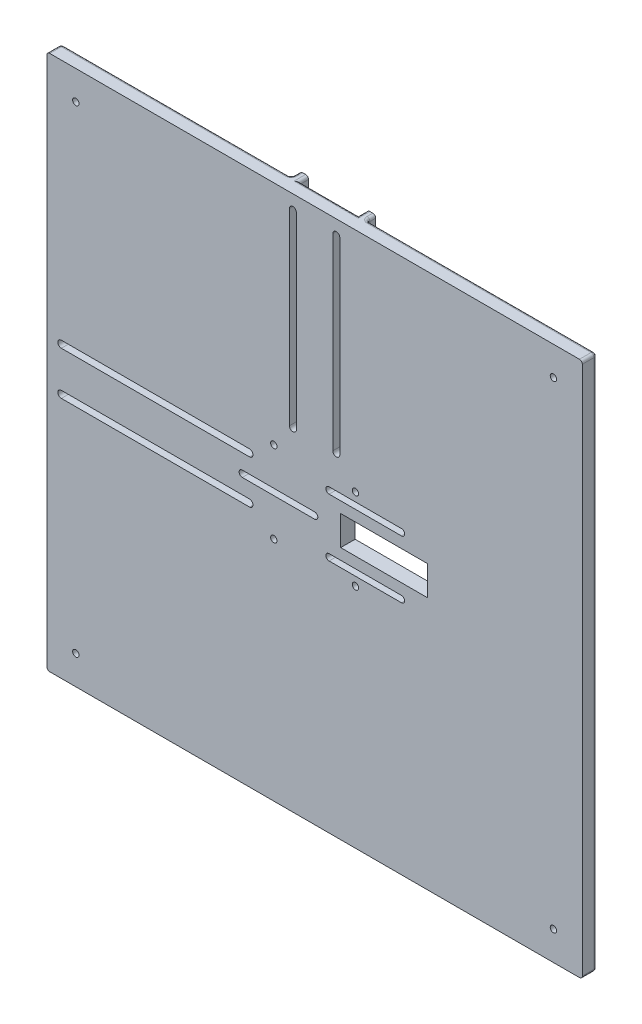
SolidWorks part; units mm, degrees
ref_plane "Plan de face" through (0, 0, 0) normal (0, 0, 1) x (1, 0, 0)
ref_plane "Plan de dessus" through (0, 0, 0) normal (0, 1, 0) x (1, 0, 0)
ref_plane "Plan de droite" through (0, 0, 0) normal (1, 0, 0) x (0, 0, -1)
sketch "Esquisse1" plane through (0, 0, 0) normal (0, 0, 1) x (1, 0, 0)
  line L1 (-92.5, 92.5) -> (92.5, 92.5)
  line L2 (-92.5, 92.5) -> (-92.5, -92.5)
  line L3 (-92.5, -92.5) -> (92.5, -92.5)
  line L4 (92.5, 92.5) -> (92.5, -92.5)
  dimension "D1" = 185
  dimension "D2" = 185
  dimension "D3" = 92.5
  dimension "D4" = 92.5
extrude "Boss.-Extru.1" add sketch "Esquisse1" along normal blind 5
sketch "Esquisse2" plane through (0, 0, 0) normal (0, 0, -1) x (-1, 0, 0)
  line L1 (22.5, 10.1) -> (92.5, 10.1)
  line L4 (92.5, 10.1) -> (92.5, 13.1)
  line L5 (92.5, -13.1) -> (22.5, -13.1)
  line L6 (92.5, -13.1) -> (92.5, -10.1)
  line L7 (92.5, -10.1) -> (22.5, -10.1)
  line L19 (92.5, 92.5) -> (92.5, -92.5) construction
  line L24 (13.1, 22.5) -> (13.1, 92.5)
  line L25 (-92.5, 92.5) -> (92.5, 92.5) construction
  line L26 (10.1, 22.5) -> (10.1, 92.5)
  line L28 (-13.1, 92.5) -> (-10.1, 92.5)
  line L29 (10.1, 92.5) -> (13.1, 92.5)
  line L31 (-10.1, 92.5) -> (-10.1, 22.5)
  line L32 (-13.1, 92.5) -> (-13.1, 22.5)
  line L33 (-10.1, 22.5) -> (-13.1, 22.5)
  line L35 (22.5, -10.1) -> (22.5, -13.1)
  line L36 (92.5, 13.1) -> (22.5, 13.1)
  line L37 (22.5, 13.1) -> (22.5, 10.1)
  line L38 (13.1, 22.5) -> (10.1, 22.5)
  dimension "D1" = 20.2
  dimension "D2" = 3
  dimension "D3" = 3
  dimension "D4" = 10.1
  dimension "D5" = 3
  dimension "D6" = 3
  dimension "D7" = 20.2
  dimension "D8" = 10.1
  dimension "D9" = 70
  dimension "D10" = 70
extrude "Boss.-Extru.2" add sketch "Esquisse2" along normal blind 3
fillet "Congé1" radius 1 32 edges at (-13.1, 57.5, 0) (-57.5, -13.1, 0) (-13.1, 92.5, -1.5) (-92.5, -13.1, -1.5) (92.5, -92.5, 2.5) (92.5, 92.5, 2.5) (92.5, 0, 0) (0, 92.5, 0) (-92.5, 0, 0) (-52.8, 92.5, 0) (-92.5, 52.8, 0) (-92.5, 92.5, 2.5) (52.8, 92.5, 0) (0, -92.5, 0) (-92.5, -52.8, 0) (-92.5, -92.5, 2.5) (-10.1, 92.5, -1.5) (-92.5, 10.1, -1.5) (-92.5, -10.1, -1.5) (13.1, 92.5, -1.5) (10.1, 92.5, -1.5) (13.1, 57.5, 0) (-92.5, 13.1, -1.5) (-57.5, 13.1, 0) (-22.5, -11.6, 0) (11.6, 22.5, 0) (-11.6, 22.5, 0) (-22.5, 11.6, 0) (-22.5, -13.1, -1.5) (13.1, 22.5, -1.5) (-13.1, 22.5, -1.5) (-22.5, 13.1, -1.5)
sketch "Esquisse4" plane through (0, 0, 0) normal (0, 0, -1) x (-1, 0, 0)
  line L4 (-92.5, -91.5) -> (-92.5, 91.5) construction
  line L5 (91.5, -92.5) -> (-91.5, -92.5) construction
  line L6 (-91.5, 92.5) -> (-14.1, 92.5) construction
  line L7 (92.5, -14.1) -> (92.5, -91.5) construction
  circle A0 centre (-14.1, 14.1) radius 1.1
  circle A1 centre (14.1, 14.1) radius 1.1
  circle A2 centre (14.1, -14.1) radius 1.1
  circle A3 centre (-14.1, -14.1) radius 1.1
  circle A4 centre (-82.5, -82.5) radius 1.1
  circle A5 centre (-82.5, 82.5) radius 1.1
  circle A6 centre (82.5, -82.5) radius 1.1
  circle A7 centre (82.5, 82.5) radius 1.1
  dimension "D1" = 2.2
  dimension "D4" = 4
  dimension "D5" = 4
  dimension "D6" = 10
  dimension "D7" = 10
  dimension "D8" = 10
  dimension "D9" = 10
  dimension "D10" = 4
  dimension "D11" = 4
extrude "Enlèv. mat.-Extru.1" cut sketch "Esquisse4" against normal up to next
sketch "Esquisse5" plane through (0, 0, 0) normal (0, 0, -1) x (-1, 0, 0)
  line L0 (-7.5, 87.5) -> (-7.5, 22.5) construction
  line L1 (-6.3, 87.5) -> (-6.3, 22.5)
  line L2 (-8.7, 87.5) -> (-8.7, 22.5)
  line L3 (7.5, 87.5) -> (7.5, 22.5) construction
  line L4 (8.7, 87.5) -> (8.7, 22.5)
  line L5 (6.3, 87.5) -> (6.3, 22.5)
  line L9 (10.1, 91.5) -> (10.1, 21.5) construction
  line L10 (-10.1, 92.5) -> (10.1, 92.5) construction
  line L11 (-10.1, 21.5) -> (-10.1, 91.5) construction
  line L12 (-91.5, 92.5) -> (-14.1, 92.5) construction
  arc A0 (-6.3, 87.5) -> (-8.7, 87.5) centre (-7.5, 87.5) ccw
  arc A1 (-8.7, 22.5) -> (-6.3, 22.5) centre (-7.5, 22.5) ccw
  arc A2 (8.7, 87.5) -> (6.3, 87.5) centre (7.5, 87.5) ccw
  arc A3 (6.3, 22.5) -> (8.7, 22.5) centre (7.5, 22.5) ccw
  point P2 (-7.5, 55)
  point P7 (7.5, 55)
  dimension "D1" = 1.2
  dimension "D2" = 1.2
  dimension "D3" = 2.6
  dimension "D4" = 5
  dimension "D6" = 2.6
  dimension "D7" = 70
extrude "Enlèv. mat.-Extru.2" cut sketch "Esquisse5" against normal through all
sketch "Esquisse6" plane through (0, 0, 0) normal (0, 0, -1) x (-1, 0, 0)
  line L0 (87.5, -7.5) -> (22.5, -7.5) construction
  line L1 (87.5, -8.7) -> (22.5, -8.7)
  line L2 (87.5, -6.3) -> (22.5, -6.3)
  line L3 (22.5, 7.5) -> (87.5, 7.5) construction
  line L4 (22.5, 8.7) -> (87.5, 8.7)
  line L5 (22.5, 6.3) -> (87.5, 6.3)
  line L6 (91.5, -10.1) -> (21.5, -10.1) construction
  line L7 (21.5, 10.1) -> (91.5, 10.1) construction
  line L8 (92.5, 10.1) -> (92.5, -10.1) construction
  arc A0 (87.5, -8.7) -> (87.5, -6.3) centre (87.5, -7.5) ccw
  arc A1 (22.5, -6.3) -> (22.5, -8.7) centre (22.5, -7.5) ccw
  arc A2 (22.5, 8.7) -> (22.5, 6.3) centre (22.5, 7.5) ccw
  arc A3 (87.5, 6.3) -> (87.5, 8.7) centre (87.5, 7.5) ccw
  point P2 (55, -7.5)
  point P7 (55, 7.5)
  dimension "D1" = 1.2
  dimension "D2" = 1.2
  dimension "D3" = 2.6
  dimension "D4" = 2.6
  dimension "D5" = 5
  dimension "D7" = 70
extrude "Enlèv. mat.-Extru.3" cut sketch "Esquisse6" against normal up to next
sketch "Esquisse9" plane through (0, 0, 5) normal (0, 0, 1) x (1, 0, 0)
  line L0 (-25, 0) -> (0, 0) construction
  line L1 (-25, 1.1) -> (0, 1.1)
  line L2 (-25, -1.1) -> (0, -1.1)
  line L3 (5, 10) -> (30, 10) construction
  line L4 (5, 11.1) -> (30, 11.1)
  line L5 (5, 8.9) -> (30, 8.9)
  line L6 (5, -10) -> (30, -10) construction
  line L7 (5, -8.9) -> (30, -8.9)
  line L8 (5, -11.1) -> (30, -11.1)
  arc A0 (-25, 1.1) -> (-25, -1.1) centre (-25, 0) ccw
  arc A1 (0, -1.1) -> (0, 1.1) centre (0, 0) ccw
  arc A2 (5, 11.1) -> (5, 8.9) centre (5, 10) ccw
  arc A3 (30, 8.9) -> (30, 11.1) centre (30, 10) ccw
  arc A4 (5, -8.9) -> (5, -11.1) centre (5, -10) ccw
  arc A5 (30, -11.1) -> (30, -8.9) centre (30, -10) ccw
  point P3 (-12.5, 0)
  point P8 (17.5, 10)
  point P15 (17.5, -10)
  point P22 (0, 0)
  dimension "D4" = 25
  dimension "D5" = 30
  dimension "D1" = 2.2
  dimension "D2" = 2.2
  dimension "D3" = 2.2
  dimension "D6" = 25
  dimension "D7" = 10
  dimension "D8" = 10
  dimension "D9" = 25
extrude "Enlèv. mat.-Extru.5" cut sketch "Esquisse9" against normal up to next
sketch "Esquisse11" plane through (0, 0, 0) normal (0, 0, -1) x (-1, 0, 0)
  line L1 (-9, 5.1) -> (-39, 5.1)
  line L2 (-9, 5.1) -> (-9, -5.1)
  line L3 (-9, -5.1) -> (-39, -5.1)
  line L4 (-39, 5.1) -> (-39, -5.1)
  dimension "D1" = 9
  dimension "D2" = 10.2
  dimension "D3" = 5.1
  dimension "D4" = 30
extrude "Enlèv. mat.-Extru.7" cut sketch "Esquisse11" against normal up to next
sketch "Esquisse12" plane through (0, 0, 0) normal (0, 0, -1) x (-1, 0, 0)
  line L1 (-33, 12.1) -> (-2, 12.1)
  line L2 (-33, 12.1) -> (-33, 7.8)
  line L3 (-33, 7.8) -> (-2, 7.8)
  line L4 (-2, 12.1) -> (-2, 7.8)
  line L5 (-33, -7.9) -> (-2, -7.9)
  line L6 (-33, -7.9) -> (-33, -12.2)
  line L7 (-33, -12.2) -> (-2, -12.2)
  line L8 (-2, -7.9) -> (-2, -12.2)
  line L9 (-3, 2.1) -> (28, 2.1)
  line L10 (-3, 2.1) -> (-3, -2.2)
  line L11 (-3, -2.2) -> (28, -2.2)
  line L12 (28, 2.1) -> (28, -2.2)
  arc A0 (-30, 11.1) -> (-30, 8.9) centre (-30, 10) ccw construction
  arc A1 (-30, -8.9) -> (-30, -11.1) centre (-30, -10) ccw construction
  arc A2 (-5, -11.1) -> (-5, -8.9) centre (-5, -10) ccw construction
  arc A3 (0, 1.1) -> (0, -1.1) centre (0, 0) ccw construction
  arc A4 (25, -1.1) -> (25, 1.1) centre (25, 0) ccw construction
  arc A5 (-5, 8.9) -> (-5, 11.1) centre (-5, 10) ccw construction
  point P15 (-31.1, 10)
  point P20 (-31.1, -10)
  dimension "D7" = 3
  dimension "D8" = 3
  dimension "D9" = 3
  dimension "D10" = 3
  dimension "D11" = 3
  dimension "D12" = 3
  dimension "D1" = 2.1
  dimension "D2" = 4.3
  dimension "D3" = 2.1
  dimension "D4" = 4.3
  dimension "D5" = 2.1
  dimension "D6" = 4.3
extrude "Enlèv. mat.-Extru.9" cut sketch "Esquisse12" against normal blind 2
fillet "Congé2" radius 0.5 11 edges at (33, -12.2, 1) (33, -7.9, 1) (2, -7.9, 1) (2, -12.2, 1) (-28, -2.2, 1) (-28, 2.1, 1) (3, -2.2, 1) (3, 2.1, 1) (2, 12.1, 1) (33, 7.8, 1) (33, 12.1, 1)
sketch "Esquisse13" plane through (0, 0, 0) normal (0, 0, -1) x (-1, 0, 0)
  line L0 (-14.1, 91.5) -> (-91.5, 91.5) construction
  line L1 (-80, -82.5) -> (-81.25, -80.3349)
  line L2 (-81.25, -80.3349) -> (-83.75, -80.3349)
  line L3 (-83.75, -80.3349) -> (-85, -82.5)
  line L4 (-85, -82.5) -> (-83.75, -84.6651)
  line L5 (-83.75, -84.6651) -> (-81.25, -84.6651)
  line L6 (-81.25, -84.6651) -> (-80, -82.5)
  line L7 (83.75, -84.6651) -> (85, -82.5)
  line L8 (85, -82.5) -> (83.75, -80.3349)
  line L9 (83.75, -80.3349) -> (81.25, -80.3349)
  line L10 (81.25, -80.3349) -> (80, -82.5)
  line L11 (80, -82.5) -> (81.25, -84.6651)
  line L12 (81.25, -84.6651) -> (83.75, -84.6651)
  line L13 (85, 82.5) -> (83.75, 84.6651)
  line L14 (83.75, 84.6651) -> (81.25, 84.6651)
  line L15 (81.25, 84.6651) -> (80, 82.5)
  line L16 (80, 82.5) -> (81.25, 80.3349)
  line L17 (81.25, 80.3349) -> (83.75, 80.3349)
  line L18 (83.75, 80.3349) -> (85, 82.5)
  line L19 (-80, 82.5) -> (-81.25, 84.6651)
  line L20 (-81.25, 84.6651) -> (-83.75, 84.6651)
  line L21 (-83.75, 84.6651) -> (-85, 82.5)
  line L22 (-85, 82.5) -> (-83.75, 80.3349)
  line L23 (-83.75, 80.3349) -> (-81.25, 80.3349)
  line L24 (-81.25, 80.3349) -> (-80, 82.5)
  line L25 (91.5, 91.5) -> (14.1, 91.5) construction
  line L26 (-91.5, -91.5) -> (91.5, -91.5) construction
  circle A0 centre (-82.5, -82.5) radius 2.1651 construction
  circle A1 centre (82.5, -82.5) radius 2.1651 construction
  circle A2 centre (82.5, 82.5) radius 2.1651 construction
  circle A3 centre (-82.5, 82.5) radius 2.1651 construction
  dimension "D1" = 2.5
  dimension "D2" = 2.5
  dimension "D3" = 2.5
  dimension "D4" = 2.5
extrude "Enlèv. mat.-Extru.10" cut sketch "Esquisse13" against normal blind 2
